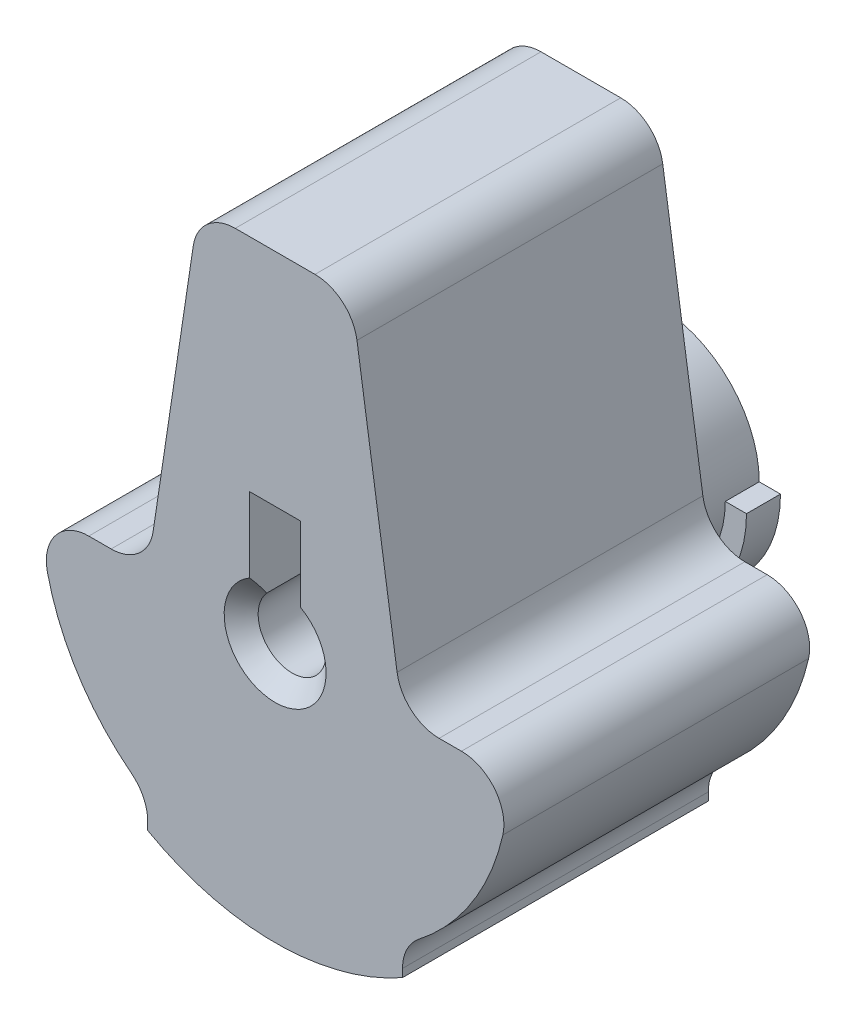
SolidWorks part; units mm, degrees
ref_plane "Front Plane" through (0, 0, 0) normal (0, 0, 1) x (1, 0, 0)
ref_plane "Top Plane" through (0, 0, 0) normal (0, 1, 0) x (1, 0, 0)
ref_plane "Right Plane" through (0, 0, 0) normal (1, 0, 0) x (0, 0, -1)
sketch "Sketch2" plane through (0, 0, 0) normal (0, 0, 1) x (1, 0, 0)
  line L5 (-0.762, 0) -> (0.762, 0)
  line L6 (-3.81, 0) -> (3.81, 0)
  line L13 (-3.81, 0) -> (-3.81, 8.636)
  line L14 (-2.286, 10.16) -> (2.286, 10.16)
  line L15 (3.81, 0) -> (3.81, 8.636)
  line L16 (-0.762, 0) -> (-0.762, 3.556)
  line L17 (-0.762, 3.556) -> (0.762, 3.556)
  line L18 (0.762, 0) -> (0.762, 3.556)
  circle A0 centre (0, 0) radius 1.524
  circle A1 centre (0, 0) radius 1.016
  circle A2 centre (0, 0) radius 3.81
  arc A3 (3.81, 8.636) -> (2.286, 10.16) centre (2.286, 8.636) ccw
  arc A4 (-3.81, 8.636) -> (-2.286, 10.16) centre (-2.286, 8.636) cw
  point P0 (0, 0)
  point P5 (0, 0)
  dimension "D1" = 2.032
  dimension "D2" = 3.048
  dimension "D5" = 7.62
  dimension "D7" = 1.524
  dimension "D3" = 1.524
  dimension "D4" = 3.556
  dimension "D6" = 10.16
extrude "Boss-Extrude2" add sketch "Sketch2" along normal blind 9.144 contours L6 A2 A0 | A1 L6 A0 | A1 L6 A0 L18 | A1 L18 A0 L16 | A1 L16 A0 L6 | L16 A2 L6 A0 | L18 A2 L16 A0 | L6 A2 L18 A0 | A2 L15 L14 L13 L16 L17 L18 | A2 L18 L17 L16
sketch "Sketch3" plane through (0, 0, 9.144) normal (0, 0, 1) x (1, 0, 0)
  line L4 (-3.81, 0) -> (3.81, 0)
  line L5 (-3.81, 8.636) -> (-3.81, 0)
  line L6 (2.286, 10.16) -> (-2.286, 10.16)
  line L7 (3.81, 0) -> (3.81, 8.636)
  line L8 (-3.81, 0) -> (3.81, 0)
  line L9 (-3.81, 8.636) -> (-3.81, 0)
  line L10 (2.286, 10.16) -> (-2.286, 10.16)
  line L11 (3.81, 0) -> (3.81, 8.636)
  line L12 (-0.762, 0) -> (0.762, 0)
  line L13 (-0.762, 3.556) -> (-0.762, 0)
  line L14 (0.762, 3.556) -> (-0.762, 3.556)
  line L15 (0.762, 0) -> (0.762, 3.556)
  line L16 (-0.762, 0) -> (0.762, 0)
  line L17 (-0.762, 3.556) -> (-0.762, 0)
  line L18 (0.762, 3.556) -> (-0.762, 3.556)
  line L19 (0.762, 0) -> (0.762, 3.556)
  circle A1 centre (0, 0) radius 3.81
  circle A2 centre (0, 0) radius 3.81
  circle A3 centre (0, 0) radius 1.016
  circle A4 centre (0, 0) radius 1.016
  circle A5 centre (0, 0) radius 1.524
  circle A6 centre (0, 0) radius 1.524
  arc A8 (3.81, 8.636) -> (2.286, 10.16) centre (2.286, 8.636) ccw
  arc A9 (3.81, 8.636) -> (2.286, 10.16) centre (2.286, 8.636) ccw
  arc A10 (-2.286, 10.16) -> (-3.81, 8.636) centre (-2.286, 8.636) ccw
  arc A11 (-2.286, 10.16) -> (-3.81, 8.636) centre (-2.286, 8.636) ccw
  arc M16 (1.016, 0) -> (-0.762, 0.672) centre (0, 0) cw
  dimension "D1" = 0
  dimension "D2" = 0
  dimension "D3" = 0
  dimension "D4" = 0
  dimension "D5" = 0
extrude "Cut-Extrude1" cut sketch "Sketch3" against normal blind 0.508 contours A2 L19 L18 L17 | L19 A6 L17 M16 | A4
sketch "Sketch4" plane through (0, 0, 0) normal (0, 0, -1) x (-1, 0, 0)
  line L3 (3.81, 0) -> (3.81, 8.636)
  line L4 (2.286, 10.16) -> (-2.286, 10.16)
  line L5 (-3.81, 8.636) -> (-3.81, 0)
  line L6 (3.81, 0) -> (3.81, 8.636)
  line L7 (2.286, 10.16) -> (-2.286, 10.16)
  line L8 (-3.81, 8.636) -> (-3.81, 0)
  line L10 (-3.81, 0) -> (3.81, 0)
  line L11 (3.81, 0) -> (3.81, 8.636)
  line L12 (2.286, 10.16) -> (-2.286, 10.16)
  line L13 (-3.81, 8.636) -> (-3.81, 0)
  line L14 (-3.81, 0) -> (3.81, 0)
  line L15 (3.81, 0) -> (3.81, 8.636)
  line L16 (2.286, 10.16) -> (-2.286, 10.16)
  line L17 (-3.81, 8.636) -> (-3.81, 0)
  line L18 (-0.762, 0) -> (0.762, 0)
  line L19 (0.762, 0) -> (0.762, 3.556)
  line L20 (0.762, 3.556) -> (-0.762, 3.556)
  line L21 (-0.762, 3.556) -> (-0.762, 0)
  line L22 (-0.762, 0) -> (0.762, 0)
  line L23 (0.762, 0) -> (0.762, 3.556)
  line L24 (0.762, 3.556) -> (-0.762, 3.556)
  line L25 (-0.762, 3.556) -> (-0.762, 0)
  arc A1 (-3.81, 0) -> (3.81, 0) centre (0, 0) ccw
  arc A2 (-3.81, 0) -> (3.81, 0) centre (0, 0) ccw
  circle A3 centre (0, 0) radius 3.81
  circle A4 centre (0, 0) radius 3.81
  circle A5 centre (0, 0) radius 1.016
  circle A6 centre (0, 0) radius 1.016
  circle A7 centre (0, 0) radius 1.524
  circle A8 centre (0, 0) radius 1.524
  arc A10 (-2.286, 10.16) -> (-3.81, 8.636) centre (-2.286, 8.636) ccw
  arc A11 (3.81, 8.636) -> (2.286, 10.16) centre (2.286, 8.636) ccw
  arc A12 (3.81, 8.636) -> (2.286, 10.16) centre (2.286, 8.636) ccw
  arc A13 (-2.286, 10.16) -> (-3.81, 8.636) centre (-2.286, 8.636) ccw
  arc A14 (-2.286, 10.16) -> (-3.81, 8.636) centre (-2.286, 8.636) ccw
  arc A15 (-2.286, 10.16) -> (-3.81, 8.636) centre (-2.286, 8.636) ccw
  arc A16 (3.81, 8.636) -> (2.286, 10.16) centre (2.286, 8.636) ccw
  arc A17 (3.81, 8.636) -> (2.286, 10.16) centre (2.286, 8.636) ccw
  arc M20 (0.762, 0.672) -> (-1.016, 0) centre (0, 0) cw
  dimension "D1" = 0
  dimension "D2" = 0
  dimension "D3" = 0
  dimension "D4" = 0
  dimension "D5" = 0
  dimension "D6" = 0
extrude "Cut-Extrude2" cut sketch "Sketch4" against normal through all contours A8 L23 A4 L25 | L23 A8 L25 M20
sketch "Sketch7" plane through (0, 0, 0) normal (0, 1, 0) x (1, 0, 0)
  line L0 (0, 0) -> (0, -9.144)
  line L1 (-2.286, -9.144) -> (2.286, -9.144) construction
  line L2 (0, -9.144) -> (1.524, -9.144)
  line L3 (1.524, -9.144) -> (1.016, -8.636)
  line L4 (1.016, -8.636) -> (1.016, -0.508)
  line L5 (1.016, -0.508) -> (1.524, 0)
  line L6 (-2.286, 0) -> (2.286, 0) construction
  line L7 (1.524, 0) -> (0, 0)
  point P5 (1.016, -4.572)
  point P12 (0, -4.572)
  dimension "D1" = 1.016
  dimension "D2" = 45
  dimension "D4" = 1.524
revolve "Cut-Revolve1" cut sketch "Sketch7" angle 360 about L0
sketch "Sketch10" plane through (0, 0, 9.144) normal (0, 0, 1) x (1, 0, 0)
  line L0 (-6.985, 0) -> (6.985, 0)
  line L1 (-0.762, 3.556) -> (-0.762, 1.3198) construction
  line L2 (-0.762, 3.556) -> (-0.762, 1.3198)
  line L3 (0.762, 1.3198) -> (0.762, 3.556) construction
  line L4 (3.81, 0) -> (3.81, 8.636)
  line L5 (3.81, 0) -> (3.81, 8.636)
  line L6 (2.286, 10.16) -> (-2.286, 10.16)
  line L9 (2.286, 10.16) -> (-2.286, 10.16)
  line L10 (-3.81, 8.636) -> (-3.81, 0)
  line L11 (-3.81, 8.636) -> (-3.81, 0)
  line L12 (0.762, 1.3198) -> (0.762, 3.556)
  line L13 (0.762, 3.556) -> (-0.762, 3.556) construction
  line L14 (0.762, 3.556) -> (-0.762, 3.556)
  circle A0 centre (0, 0) radius 6.985
  arc A1 (-0.762, 1.3198) -> (0.762, 1.3198) centre (0, 0) ccw construction
  arc A2 (-3.81, 0) -> (3.81, 0) centre (0, 0) ccw
  arc A3 (-3.81, 0) -> (3.81, 0) centre (0, 0) ccw
  arc A4 (-0.762, 1.3198) -> (0.762, 1.3198) centre (0, 0) ccw
  arc A6 (3.81, 8.636) -> (2.286, 10.16) centre (2.286, 8.636) ccw
  arc A7 (3.81, 8.636) -> (2.286, 10.16) centre (2.286, 8.636) ccw
  arc A8 (-2.286, 10.16) -> (-3.81, 8.636) centre (-2.286, 8.636) ccw
  arc A9 (-2.286, 10.16) -> (-3.81, 8.636) centre (-2.286, 8.636) ccw
  arc M7 (-3.81, 0) -> (3.81, 0) centre (0, 0) ccw
  dimension "D1" = 13.97
  dimension "D2" = 0
extrude "Boss-Extrude8" add sketch "Sketch10" against normal up to surface (9.144 mm away) contours L0 A0 M7 | A3 L5 A7 L9 A9 L11 | L14 L2 A4 L12
sketch "Sketch14" plane through (0, 0, 9.144) normal (0, 0, 1) x (1, 0, 0)
  line L0 (-3.81, 0) -> (-3.81, -6.7454)
  line L1 (3.81, 0) -> (3.81, -6.7454)
  line L5 (-3.81, 8.636) -> (-3.81, 0)
  line L8 (3.81, 0) -> (3.81, 8.636)
  line L9 (2.286, 10.16) -> (-2.286, 10.16)
  line L10 (-3.81, 8.636) -> (-3.81, 0)
  line L13 (3.81, 0) -> (3.81, 8.636)
  line L14 (2.286, 10.16) -> (-2.286, 10.16)
  line L15 (-3.81, 0) -> (-6.985, 0)
  line L16 (-3.81, 0) -> (-6.985, 0)
  line L17 (6.985, 0) -> (3.81, 0)
  line L18 (6.985, 0) -> (3.81, 0)
  circle A0 centre (0, 0) radius 7.747
  arc A3 (-6.985, 0) -> (6.985, 0) centre (0, 0) ccw
  arc A4 (3.81, 8.636) -> (2.286, 10.16) centre (2.286, 8.636) ccw
  arc A5 (-2.286, 10.16) -> (-3.81, 8.636) centre (-2.286, 8.636) ccw
  arc A7 (3.81, 8.636) -> (2.286, 10.16) centre (2.286, 8.636) ccw
  arc A8 (-2.286, 10.16) -> (-3.81, 8.636) centre (-2.286, 8.636) ccw
  arc A10 (-6.985, 0) -> (6.985, 0) centre (0, 0) ccw
  arc M16 (-6.985, 0) -> (6.985, 0) centre (0, 0) ccw
  dimension "D2" = 15.494
  dimension "D1" = 0
extrude "Boss-Extrude10" add sketch "Sketch14" against normal up to surface (9.144 mm away) contours L0 A0 L1 M16 up to face at (0, 1.727, 0)
fillet "Fillet2" radius 1.27 2 edges at (-6.985, 0, 4.572) (6.985, 0, 4.572)
sketch "Sketch16" plane through (0, 0, 9.144) normal (0, 0, 1) x (1, 0, 0)
  line L0 (-3.81, 0) -> (-2.286, 10.16)
  line L1 (2.286, 10.16) -> (3.81, 0)
  line L8 (-3.81, -5.8544) -> (-3.81, -6.7454)
  line L9 (3.81, -6.7454) -> (3.81, -5.8544)
  line L11 (-3.81, 0) -> (-5.5721, 0)
  line L12 (2.286, 10.16) -> (-2.286, 10.16)
  line L13 (-3.81, 0) -> (-5.5721, 0)
  line L15 (-3.81, -5.8544) -> (-3.81, -6.7454)
  line L16 (3.81, -6.7454) -> (3.81, -5.8544)
  line L19 (2.286, 10.16) -> (-2.286, 10.16)
  line L21 (5.5721, 0) -> (3.81, 0)
  line L22 (5.5721, 0) -> (3.81, 0)
  line L23 (3.81, 0) -> (3.81, 8.636)
  line L24 (3.81, 0) -> (3.81, 8.636)
  line L25 (-3.81, 8.636) -> (-3.81, 0)
  line L26 (-3.81, 8.636) -> (-3.81, 0)
  arc A7 (-5.5721, 0) -> (-6.8103, -1.5522) centre (-5.5721, -1.27) ccw
  arc A8 (-5.5721, 0) -> (-6.8103, -1.5522) centre (-5.5721, -1.27) ccw
  arc A9 (-3.81, -6.7454) -> (3.81, -6.7454) centre (0, 0) ccw
  arc A10 (-6.8103, -1.5522) -> (-3.81, -5.8544) centre (0, 0) ccw
  arc A11 (-6.8103, -1.5522) -> (-3.81, -5.8544) centre (0, 0) ccw
  arc A12 (3.81, 8.636) -> (2.286, 10.16) centre (2.286, 8.636) ccw
  arc A13 (-2.286, 10.16) -> (-3.81, 8.636) centre (-2.286, 8.636) ccw
  arc A16 (-3.81, -6.7454) -> (3.81, -6.7454) centre (0, 0) ccw
  arc A19 (3.81, 8.636) -> (2.286, 10.16) centre (2.286, 8.636) ccw
  arc A20 (-2.286, 10.16) -> (-3.81, 8.636) centre (-2.286, 8.636) ccw
  arc A21 (3.81, -5.8544) -> (6.8103, -1.5522) centre (0, 0) ccw
  arc A22 (3.81, -5.8544) -> (6.8103, -1.5522) centre (0, 0) ccw
  arc A23 (6.8103, -1.5522) -> (5.5721, 0) centre (5.5721, -1.27) ccw
  arc A24 (6.8103, -1.5522) -> (5.5721, 0) centre (5.5721, -1.27) ccw
  line M28 (3.81, 0) -> (3.81, 8.636)
  arc M29 (3.81, 8.636) -> (2.286, 10.16) centre (2.286, 8.636) ccw
  arc M31 (-2.286, 10.16) -> (-3.81, 8.636) centre (-2.286, 8.636) ccw
  line M32 (-3.81, 8.636) -> (-3.81, 0)
  dimension "D1" = 0
extrude "Cut-Extrude4" cut sketch "Sketch16" against normal up to surface (9.144 mm away) contours L0 M32 M31 | L1 M29 M28 up to face at (0, 1.727, 0)
fillet "Fillet4" radius 1.27 6 edges at (-3.81, -5.8544, 4.572) (3.81, -5.8544, 4.572) (3.81, 0, 4.572) (-3.81, 0, 4.572) (2.286, 10.16, 4.572) (-2.286, 10.16, 4.572)
sketch "Sketch17" plane through (0, 0, 0) normal (0, 0, -1) x (-1, 0, 0)
  line L0 (0.762, 1.3198) -> (0.762, 3.556) construction
  line L1 (0.762, 1.3198) -> (0.762, 3.556)
  line L2 (-0.762, 3.556) -> (-0.762, 1.3198) construction
  line L3 (-0.762, 3.556) -> (-0.762, 1.3198)
  line L4 (0.762, 1.3198) -> (0.762, 0.672) construction
  line L5 (-0.762, 0.672) -> (-0.762, 1.3198) construction
  line L6 (0.762, 1.3198) -> (0.762, 0.672)
  line L7 (1.1923, 10.16) -> (-1.1923, 10.16)
  line L8 (-0.762, 0.672) -> (-0.762, 1.3198)
  line L10 (-3.81, -6.5068) -> (-3.81, -6.7454)
  line L11 (3.81, -6.7454) -> (3.81, -6.5068)
  line L12 (-2.4482, 9.0784) -> (-3.6478, 1.0816)
  line L13 (-2.4482, 9.0784) -> (-3.6478, 1.0816)
  line L14 (1.1923, 10.16) -> (-1.1923, 10.16)
  line L17 (-3.81, -6.5068) -> (-3.81, -6.7454)
  line L18 (3.81, -6.7454) -> (3.81, -6.5068)
  line L21 (3.6478, 1.0816) -> (2.4482, 9.0784)
  line L22 (3.6478, 1.0816) -> (2.4482, 9.0784)
  line L25 (-4.9037, 0) -> (-5.5721, 0)
  line L27 (-4.9037, 0) -> (-5.5721, 0)
  line L29 (5.5721, 0) -> (4.9037, 0)
  line L30 (5.5721, 0) -> (4.9037, 0)
  circle A0 centre (0, 0) radius 3.048
  arc A1 (-0.762, 1.3198) -> (0.762, 1.3198) centre (0, 0) ccw construction
  arc A2 (-0.762, 1.3198) -> (0.762, 1.3198) centre (0, 0) ccw
  arc A3 (-0.762, 0.672) -> (0.762, 0.672) centre (0, 0) ccw construction
  arc A4 (-0.762, 0.672) -> (0.762, 0.672) centre (0, 0) ccw
  arc A6 (-1.1923, 10.16) -> (-2.4482, 9.0784) centre (-1.1923, 8.89) ccw
  arc A8 (-1.1923, 10.16) -> (-2.4482, 9.0784) centre (-1.1923, 8.89) ccw
  arc A10 (2.4482, 9.0784) -> (1.1923, 10.16) centre (1.1923, 8.89) ccw
  arc A11 (2.4482, 9.0784) -> (1.1923, 10.16) centre (1.1923, 8.89) ccw
  arc A16 (-5.5721, 0) -> (-6.8103, -1.5522) centre (-5.5721, -1.27) ccw
  arc A17 (-3.81, -6.7454) -> (3.81, -6.7454) centre (0, 0) ccw
  arc A19 (-5.5721, 0) -> (-6.8103, -1.5522) centre (-5.5721, -1.27) ccw
  arc A21 (6.8103, -1.5522) -> (5.5721, 0) centre (5.5721, -1.27) ccw
  arc A28 (-3.81, -6.7454) -> (3.81, -6.7454) centre (0, 0) ccw
  arc A34 (6.8103, -1.5522) -> (5.5721, 0) centre (5.5721, -1.27) ccw
  arc A36 (-6.8103, -1.5522) -> (-4.2985, -5.5058) centre (0, 0) ccw
  arc A37 (-6.8103, -1.5522) -> (-4.2985, -5.5058) centre (0, 0) ccw
  arc A38 (4.2985, -5.5058) -> (6.8103, -1.5522) centre (0, 0) ccw
  arc A39 (4.2985, -5.5058) -> (6.8103, -1.5522) centre (0, 0) ccw
  arc A44 (-4.9037, 0) -> (-3.6478, 1.0816) centre (-4.9037, 1.27) ccw
  arc A45 (-4.9037, 0) -> (-3.6478, 1.0816) centre (-4.9037, 1.27) ccw
  arc A46 (-3.81, -6.5068) -> (-4.2985, -5.5058) centre (-5.08, -6.5068) ccw
  arc A47 (-3.81, -6.5068) -> (-4.2985, -5.5058) centre (-5.08, -6.5068) ccw
  arc A48 (4.2985, -5.5058) -> (3.81, -6.5068) centre (5.08, -6.5068) ccw
  arc A49 (4.2985, -5.5058) -> (3.81, -6.5068) centre (5.08, -6.5068) ccw
  arc A50 (3.6478, 1.0816) -> (4.9037, 0) centre (4.9037, 1.27) ccw
  arc A51 (3.6478, 1.0816) -> (4.9037, 0) centre (4.9037, 1.27) ccw
  arc M2 (0.762, 1.3198) -> (-0.762, 1.3198) centre (0, 0) cw
  line M3 (-0.762, 1.3198) -> (-0.762, 3.556)
  dimension "D1" = 6.096
  dimension "D2" = 0
extrude "Boss-Extrude11" add sketch "Sketch17" along normal blind 1.27 contours A0 L1 M3 M2
sketch "Sketch18" plane through (0, 0, -1.27) normal (0, 0, -1) x (-1, 0, 0)
  line L0 (0.762, 2.9512) -> (0.762, 3.556) construction
  line L1 (-0.762, 3.556) -> (-0.762, 2.9512) construction
  line L2 (0.762, 2.9512) -> (0.762, 3.556)
  line L3 (-0.762, 3.556) -> (-0.762, 2.9512)
  line L4 (-3.683, 0) -> (3.683, 0)
  circle A0 centre (0, 0) radius 3.683
  arc A1 (-0.762, 2.9512) -> (0.762, 2.9512) centre (0, 0) ccw construction
  arc A2 (-0.762, 2.9512) -> (0.762, 2.9512) centre (0, 0) ccw
  arc A3 (-0.762, 1.3198) -> (0.762, 1.3198) centre (0, 0) ccw construction
  arc A4 (-0.762, 1.3198) -> (0.762, 1.3198) centre (0, 0) ccw
  arc M3 (-0.762, 2.9512) -> (0.762, 2.9512) centre (0, 0) ccw
  arc M13 (0.762, 1.3198) -> (-0.762, 1.3198) centre (0, 0) cw
  dimension "D1" = 7.366
extrude "Boss-Extrude12" add sketch "Sketch18" along normal blind 1.016 contours L4 M3 M13 | L4 A0 M3
sketch "Sketch20" plane through (0, 0, 0) normal (0, 0, -1) x (-1, 0, 0)
  line L0 (0.762, 1.3198) -> (0.762, 0.672) construction
  line L1 (-0.762, 0.672) -> (-0.762, 1.3198) construction
  line L2 (0.762, 1.3198) -> (0.762, 0.672)
  line L3 (-0.762, 0.672) -> (-0.762, 1.3198)
  line L7 (1.1923, 10.16) -> (-1.1923, 10.16)
  line L8 (-2.4482, 9.0784) -> (-3.6478, 1.0816)
  line L9 (-4.9037, 0) -> (-5.5721, 0)
  line L10 (-3.81, -6.5068) -> (-3.81, -6.7454)
  line L11 (3.81, -6.7454) -> (3.81, -6.5068)
  line L12 (5.5721, 0) -> (4.9037, 0)
  line L13 (3.6478, 1.0816) -> (2.4482, 9.0784)
  line L14 (1.1923, 10.16) -> (-1.1923, 10.16)
  line L15 (-2.4482, 9.0784) -> (-3.6478, 1.0816)
  line L16 (-4.9037, 0) -> (-5.5721, 0)
  line L17 (-3.81, -6.5068) -> (-3.81, -6.7454)
  line L18 (3.81, -6.7454) -> (3.81, -6.5068)
  line L19 (5.5721, 0) -> (4.9037, 0)
  line L20 (3.6478, 1.0816) -> (2.4482, 9.0784)
  arc A0 (-0.762, 0.672) -> (0.762, 0.672) centre (0, 0) ccw construction
  arc A1 (-0.762, 1.3198) -> (0.762, 1.3198) centre (0, 0) ccw construction
  arc A2 (-0.762, 0.672) -> (0.762, 0.672) centre (0, 0) ccw
  arc A3 (-0.762, 1.3198) -> (0.762, 1.3198) centre (0, 0) ccw
  arc A11 (-1.1923, 10.16) -> (-2.4482, 9.0784) centre (-1.1923, 8.89) ccw
  arc A12 (-4.9037, 0) -> (-3.6478, 1.0816) centre (-4.9037, 1.27) ccw
  arc A13 (-5.5721, 0) -> (-6.8103, -1.5522) centre (-5.5721, -1.27) ccw
  arc A14 (-6.8103, -1.5522) -> (-4.2985, -5.5058) centre (0, 0) ccw
  arc A15 (-3.81, -6.5068) -> (-4.2985, -5.5058) centre (-5.08, -6.5068) ccw
  arc A16 (-3.81, -6.7454) -> (3.81, -6.7454) centre (0, 0) ccw
  arc A17 (4.2985, -5.5058) -> (3.81, -6.5068) centre (5.08, -6.5068) ccw
  arc A18 (4.2985, -5.5058) -> (6.8103, -1.5522) centre (0, 0) ccw
  arc A19 (6.8103, -1.5522) -> (5.5721, 0) centre (5.5721, -1.27) ccw
  arc A20 (3.6478, 1.0816) -> (4.9037, 0) centre (4.9037, 1.27) ccw
  arc A21 (2.4482, 9.0784) -> (1.1923, 10.16) centre (1.1923, 8.89) ccw
  arc A22 (-1.1923, 10.16) -> (-2.4482, 9.0784) centre (-1.1923, 8.89) ccw
  arc A23 (-4.9037, 0) -> (-3.6478, 1.0816) centre (-4.9037, 1.27) ccw
  arc A24 (-5.5721, 0) -> (-6.8103, -1.5522) centre (-5.5721, -1.27) ccw
  arc A25 (-6.8103, -1.5522) -> (-4.2985, -5.5058) centre (0, 0) ccw
  arc A26 (-3.81, -6.5068) -> (-4.2985, -5.5058) centre (-5.08, -6.5068) ccw
  arc A27 (-3.81, -6.7454) -> (3.81, -6.7454) centre (0, 0) ccw
  arc A28 (4.2985, -5.5058) -> (3.81, -6.5068) centre (5.08, -6.5068) ccw
  arc A29 (4.2985, -5.5058) -> (6.8103, -1.5522) centre (0, 0) ccw
  arc A30 (6.8103, -1.5522) -> (5.5721, 0) centre (5.5721, -1.27) ccw
  arc A31 (3.6478, 1.0816) -> (4.9037, 0) centre (4.9037, 1.27) ccw
  arc A32 (2.4482, 9.0784) -> (1.1923, 10.16) centre (1.1923, 8.89) ccw
  dimension "D1" = 0
extrude "Boss-Extrude13" add sketch "Sketch20" against normal up to vertex contours L2 A2 L3 A3
sketch "Sketch21" plane through (0, 0, 0) normal (0, 0, -1) x (-1, 0, 0)
  line L2 (0.762, 1.3198) -> (0.762, 0.672)
  line L3 (-0.762, 0.672) -> (-0.762, 1.3198)
  line L4 (0.762, 1.3198) -> (0.762, 0.672)
  line L5 (-0.762, 0.672) -> (-0.762, 1.3198)
  arc A2 (-0.762, 1.3198) -> (0.762, 1.3198) centre (0, 0) ccw
  arc A3 (-0.762, 0.672) -> (0.762, 0.672) centre (0, 0) ccw
  arc A4 (-0.762, 1.3198) -> (0.762, 1.3198) centre (0, 0) ccw
  arc A5 (-0.762, 0.672) -> (0.762, 0.672) centre (0, 0) ccw
  dimension "D1" = 0
extrude "Boss-Extrude14" add sketch "Sketch21" along normal up to surface (1.27 mm away) up to face at (1.6944, 1.191, -1.27)
sketch "Sketch22" plane through (0, 0, -1.27) normal (0, 0, -1) x (-1, 0, 0)
  line L4 (0.762, 2.9512) -> (0.762, 0.672)
  line L5 (-0.762, 0.672) -> (-0.762, 2.9512)
  line L6 (-3.048, 0) -> (-1.524, 0)
  line L7 (0.762, 2.9512) -> (0.762, 0.672)
  line L9 (-0.762, 0.672) -> (-0.762, 2.9512)
  line L10 (-3.048, 0) -> (-1.524, 0)
  line L12 (1.524, 0) -> (3.048, 0)
  line L13 (1.524, 0) -> (3.048, 0)
  arc A2 (-0.762, 0.672) -> (0.762, 0.672) centre (0, 0) ccw
  arc A5 (-0.762, 2.9512) -> (-3.048, 0) centre (0, 0) ccw
  arc A7 (-0.762, 0.672) -> (0.762, 0.672) centre (0, 0) ccw
  arc A9 (-0.762, 2.9512) -> (-3.048, 0) centre (0, 0) ccw
  arc A12 (-1.524, 0) -> (1.524, 0) centre (0, 0) ccw
  arc A13 (-1.524, 0) -> (1.524, 0) centre (0, 0) ccw
  arc A14 (3.048, 0) -> (0.762, 2.9512) centre (0, 0) ccw
  arc A15 (3.048, 0) -> (0.762, 2.9512) centre (0, 0) ccw
  dimension "D1" = 0
extrude "Boss-Extrude15" add sketch "Sketch22" along normal up to surface (1.016 mm away) contours L7 A7 L9 A9 L10 A13 L13 A15 up to face at (0, -1.3018, -2.286)
sketch "Sketch23" plane through (0, 0, 0) normal (0, 1, 0) x (1, 0, 0)
  line L0 (0, 2.286) -> (0, 0)
  line L1 (1.016, 2.286) -> (-1.016, 2.286) construction
  line L2 (-1.1923, 0) -> (1.1923, 0) construction
  line L3 (0, 0) -> (0.762, 0)
  line L4 (0.762, 0) -> (0.762, 1.524)
  line L5 (0.762, 2.286) -> (0.762, 0) construction
  line L6 (0.762, 1.524) -> (1.524, 2.286)
  line L7 (3.048, 2.286) -> (0.762, 2.286) construction
  line L8 (1.524, 2.286) -> (0, 2.286)
  dimension "D1" = 1.524
  dimension "D2" = 45
revolve "Cut-Revolve2" cut sketch "Sketch23" angle 360 about L0
